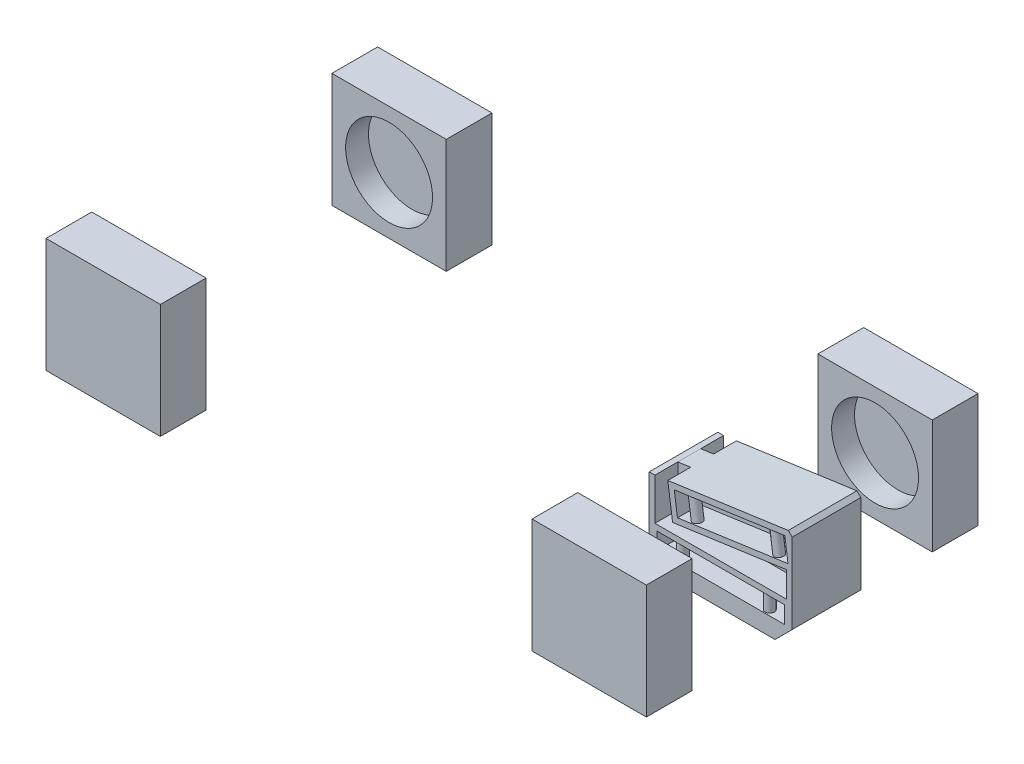
SolidWorks part; units mm, degrees
ref_plane "Front Plane" through (0, 0, 0) normal (0, 0, 1) x (1, 0, 0)
ref_plane "Top Plane" through (0, 0, 0) normal (0, 1, 0) x (1, 0, 0)
ref_plane "Right Plane" through (0, 0, 0) normal (1, 0, 0) x (0, 0, -1)
sketch "Sketch1" plane through (0, 0, 0) normal (0, 1, 0) x (1, 0, 0)
  line L0 (0, 175.6005) -> (0, -163.1385) construction
  line L1 (-212.5, -125) -> (212.5, -125)
  line L2 (-212.5, -125) -> (-212.5, 125)
  line L3 (-212.5, 125) -> (212.5, 125)
  line L4 (212.5, -125) -> (212.5, 125)
  line L5 (-212.5, -125) -> (212.5, 125) construction
  line L6 (-212.5, 125) -> (212.5, -125) construction
  line L7 (162.5, 105) -> (262.5, 105)
  line L8 (162.5, 105) -> (162.5, 145)
  line L9 (162.5, 145) -> (262.5, 145)
  line L10 (262.5, 105) -> (262.5, 145)
  line L11 (162.5, 105) -> (262.5, 145) construction
  line L12 (162.5, 145) -> (262.5, 105) construction
  line L13 (162.5, -105) -> (262.5, -105)
  line L14 (162.5, -105) -> (162.5, -145)
  line L15 (162.5, -145) -> (262.5, -145)
  line L16 (262.5, -105) -> (262.5, -145)
  line L17 (162.5, -105) -> (262.5, -145) construction
  line L18 (162.5, -145) -> (262.5, -105) construction
  line L19 (-231.0788, 0) -> (285.5483, 0) construction
  line L20 (-162.5, -145) -> (-262.5, -145)
  line L21 (-262.5, -105) -> (-262.5, -145)
  line L22 (-162.5, -105) -> (-262.5, -105)
  line L23 (-162.5, -105) -> (-162.5, -145)
  line L24 (-162.5, 145) -> (-262.5, 145)
  line L25 (-262.5, 105) -> (-262.5, 145)
  line L26 (-162.5, 105) -> (-262.5, 105)
  line L27 (-162.5, 105) -> (-162.5, 145)
  point P0 (0, 0)
  dimension "D1" = 425
  dimension "D2" = 250
  dimension "D3" = 100
  dimension "D4" = 40
  dimension "D5" = 40
  dimension "D6" = 100
extrude "Boss-Extrude1" add sketch "Sketch1" along normal mid plane 100 contours L3 L27 L24 L25 L26 L2 | L26 L27 L3 L2 | L7 L10 L9 L8 L3 L4 | L8 L7 L4 L3 | L16 L13 L4 L1 L14 L15 | L23 L1 L2 L22 L21 L20 | L23 L22 L2 L1
sketch "Sketch3" plane through (0, 0, 105) normal (0, 0, -1) x (-1, 0, 0)
  line L0 (-212.5, 50) -> (-212.5, -50) construction
  line L1 (-162.5, 50) -> (-262.5, 50) construction
  line L2 (-162.5, -50) -> (-262.5, -50) construction
  line L3 (-262.5, 0) -> (-162.5, 0) construction
  line L4 (-262.5, 50) -> (-262.5, -50) construction
  line L5 (-162.5, 50) -> (-162.5, -50) construction
  circle A0 centre (-212.5, 0) radius 38
  dimension "D1" = 76
extrude "Cut-Extrude5" cut sketch "Sketch3" against normal blind 20
sketch "Sketch4" plane through (0, 0, -105) normal (0, 0, 1) x (1, 0, 0)
  circle A0 centre (212.5, 0) radius 38 construction
  circle A1 centre (212.5, 0) radius 38
extrude "Cut-Extrude6" cut sketch "Sketch4" against normal blind 20
sketch3d "3DSketch4" plane through (0, 0, 0) normal (0, 0, 1) x (1, 0, 0)
  dimension "D1" = 8.42
sketch "Mech Trail & Caster" plane through (0, 0, 116.58) normal (0, 0, -1) x (-1, 0, 0)
  line L0 (-212.5, 38) -> (-212.5, -50) construction
  line L1 (-250.5, 0) -> (-174.5, 0) construction
  line L2 (-162.5, -50) -> (-262.5, -50) construction
  line L3 (-162.5, -50) -> (-262.5, -50)
  line L4 (-208.5, -50) -> (-212.5, -27) construction
  line L5 (-212.5, -27) -> (-225.6719, 48.7387) construction
  line L6 (-162.5, 50) -> (-262.5, 50) construction
  line L7 (-162.5, 50) -> (-262.5, 50)
  circle A0 centre (-212.5, 0) radius 38 construction
  circle A1 centre (-212.5, 0) radius 38
  point P7 (-212.5, -27)
  point P15 (-221.8913, 27)
  dimension "D1" = 23
  dimension "D2" = 4
  dimension "D3" = 23
  dimension "D4" = 9.866
sketch3d "3DSketch5"
  line L0 (212.5, 38, 116.58) -> (212.5, -50, 116.58) construction
  line L1 (250.5, 0, 116.58) -> (174.5, 0, 116.58) construction
sketch "Sketch6" plane through (221.8913, 0, 0) normal (1, 0, 0) x (0, 0, -1)
  line L0 (-116.58, 27) -> (-110.904, 27) construction
  point P0 (-116.58, 27)
  point P5 (-110.904, 27)
  dimension "D1" = 5.676
sketch3d "KPI angle/ steering axis"
  line L0 (221.8913, 27, 110.904) -> (212.5, -27, 116.58) construction
  point P0 (221.8913, 27, 110.904)
  point P2 (212.5, -27, 116.58)
sketch3d "3DSketch8" plane through (0, 0, 0) normal (0, 0, 1) x (1, 0, 0)
  dimension "D1" = 8.42
sketch "Sketch7" plane through (0, 0, -116.58) normal (0, 0, 1) x (1, 0, 0)
  line L0 (212.5, 50) -> (212.5, -50) construction
  line L1 (162.5, 50) -> (262.5, 50) construction
  line L2 (162.5, -50) -> (262.5, -50) construction
  line L3 (162.5, 0) -> (262.5, 0) construction
  line L4 (162.5, 50) -> (162.5, -50) construction
  line L5 (262.5, 50) -> (262.5, -50) construction
  line L6 (221.8913, 27) -> (212.5, -27) construction
  line L7 (221.8913, 27) -> (212.5, -27) construction
  point P12 (212.5, -27)
  point P13 (221.8913, 27)
sketch3d "3DSketch9"
  line L0 (212.5, 50, -116.58) -> (212.5, -50, -116.58) construction
  line L1 (162.5, 0, -116.58) -> (262.5, 0, -116.58) construction
sketch "Sketch8" plane through (221.8913, 0, 0) normal (-1, 0, 0) x (0, 0, 1)
  line L0 (-116.58, 27) -> (-110.91, 27) construction
  point P0 (-116.58, 27)
  point P5 (-110.91, 27)
  dimension "D1" = 5.67
sketch3d "3DSketch10"
  line L0 (221.8913, 27, -110.91) -> (212.5, -27, -116.58) construction
sketch3d "3DSketch11"
  line L0 (221.8913, 27, -116.58) -> (221.8913, 27, -110.91) construction
  line L1 (212.5, 50, -105) -> (212.5, -50, -105) construction
  line L2 (162.5, 50, -105) -> (262.5, 50, -105) construction
  line L3 (162.5, -50, -105) -> (262.5, -50, -105) construction
sketch "Front view IC's/RC" plane through (212.5, 0, 0) normal (-1, 0, 0) x (0, 0, 1)
  line L0 (-110.91, 27) -> (-89.7206, 27) construction
  line L1 (-110.91, 27) -> (285.7, -26.9974) construction
  line L2 (110.904, 27) -> (85.1327, 27) construction
  line L3 (110.904, 27) -> (-285.706, -26.9974) construction
  line L4 (-125, 50) -> (-125, -50) construction
  line L5 (-105, 50) -> (-145, 50) construction
  line L6 (-105, -50) -> (-145, -50) construction
  line L7 (125, 50) -> (125, -50) construction
  line L8 (105, 50) -> (145, 50) construction
  line L9 (105, -50) -> (145, -50) construction
  line L10 (-285.706, -26.9974) -> (285.7, -26.9974) construction
  line L11 (-125, -50) -> (285.7, -26.9974) construction
  line L12 (-285.706, -26.9974) -> (125, -50) construction
  line L13 (0, 78.2039) -> (0, -138.8888) construction
  point P20 (-116.58, -27)
  point P21 (116.58, -27)
  point P29 (0, -42.999)
  dimension "D1" = 7.753
  dimension "D2" = 396.61
  dimension "D3" = 7.753
  dimension "D4" = 396.61
  dimension "D5" = 7.001
  dimension "D6" = 410.706
sketch3d "3DSketch12" plane through (0, 0, 0) normal (0, 0, 1) x (1, 0, 0)
  dimension "D1" = 20
sketch "Left side IC's/PC" plane through (0, 0, -125) normal (0, 0, -1) x (-1, 0, 0)
  line L0 (162.5, -50) -> (262.5, -50) construction
  line L1 (162.5, 50) -> (262.5, 50) construction
  line L2 (162.5, -50) -> (262.5, -50)
  line L3 (162.5, 50) -> (262.5, 50)
  line L4 (212.5, 50) -> (212.5, -50) construction
  line L5 (162.5, 0) -> (262.5, 0) construction
  line L6 (162.5, 50) -> (162.5, -50) construction
  line L7 (262.5, 50) -> (262.5, -50) construction
  line L8 (-212.5, 50) -> (-212.5, -50) construction
  line L9 (-212.5, 50) -> (-212.5, -50) construction
  line L10 (-393.1005, -27) -> (329.5904, -27) construction
  line L11 (-221.8913, 27) -> (400.1441, -57.6885) construction
  line L12 (-221.8913, 27) -> (-156.9239, 27) construction
  line L13 (212.5, 27) -> (-344.6875, -61.2498) construction
  line L14 (212.5, 27) -> (147.1014, 27) construction
  line L15 (-212.5, -50) -> (174.7378, -27) construction
  line L16 (-128.4426, -27) -> (212.5, -50) construction
  point P12 (212.5, 27)
  point P13 (212.5, -27)
  point P14 (-212.5, -27)
  point P18 (13.51, -36.5761)
  point P27 (-128.4426, -27)
  point P29 (174.7378, -27)
  point P33 (-221.8913, 27)
  dimension "D1" = 23
  dimension "D2" = 54
  dimension "D3" = 7.753
  dimension "D4" = 9
  dimension "D5" = 340.9426
  dimension "D6" = 387.2378
  dimension "D7" = 13.4239
  dimension "D8" = 226.01
sketch3d "3DSketch13" plane through (0, 0, 0) normal (0, 0, 1) x (1, 0, 0)
  dimension "D1" = 20
sketch "Right side IC's/PC" plane through (0, 0, 125) normal (0, 0, -1) x (-1, 0, 0)
  line L0 (212.5, 50) -> (212.5, -50) construction
  line L1 (-221.8913, 27) -> (309.2663, -45.3157) construction
  line L2 (-221.8913, 27) -> (-150.1998, 27) construction
  line L3 (212.5, 27) -> (-297.8803, -53.8363) construction
  line L4 (162.5, -50) -> (262.5, -50)
  line L5 (262.5, -50) -> (262.5, 50)
  line L6 (262.5, 50) -> (162.5, 50)
  line L7 (162.5, 50) -> (162.5, -50)
  line L8 (162.5, -50) -> (262.5, -50)
  line L9 (262.5, -50) -> (262.5, 50)
  line L10 (262.5, 50) -> (162.5, 50)
  line L11 (162.5, 50) -> (162.5, -50)
  line L12 (212.5, 27) -> (139.4199, 27) construction
  line L13 (-212.5, -27) -> (212.5, -27) construction
  line L20 (-212.5, 50) -> (-212.5, -50) construction
  line L21 (-212.5, -50) -> (174.7378, -27) construction
  line L22 (212.5, -50) -> (-128.4426, -27) construction
  point P6 (212.5, -27)
  point P7 (212.5, 27)
  point P8 (-221.8913, 27)
  point P10 (174.7378, -27)
  point P24 (13.51, -36.5761)
  point P29 (-128.4426, -27)
  dimension "D2" = 23
  dimension "D3" = 54
  dimension "D4" = 7.753
  dimension "D5" = 9
  dimension "D6" = 340.9426
  dimension "D7" = 387.2378
  dimension "D8" = 13.4239
  dimension "D1" = 0
sketch3d "3DSketch14" plane through (0, 0, 0) normal (0, 0, 1) x (1, 0, 0)
  dimension "D1" = 50
sketch "Rear view IC's/RC" plane through (-212.5, 0, 0) normal (1, 0, 0) x (0, 0, -1)
  line L0 (-125, 50) -> (-125, -50) construction
  line L1 (-105, 50) -> (-145, 50) construction
  line L2 (-105, -50) -> (-145, -50) construction
  line L3 (125, 50) -> (125, -50) construction
  line L4 (105, 50) -> (145, 50) construction
  line L5 (105, -50) -> (145, -50) construction
  line L6 (0, 69.5621) -> (0, -61.9838) construction
  line L7 (-193.1722, -27) -> (206.3811, -27) construction
  line L8 (-110.91, 27) -> (114.5883, -27) construction
  line L9 (-110.91, 27) -> (-74.4999, 27) construction
  line L10 (110.91, 27) -> (79.0484, 27) construction
  line L11 (110.91, 27) -> (-114.5883, -27) construction
  line L12 (-125, -50) -> (114.5883, -27) construction
  line L13 (-114.5883, -27) -> (125, -50) construction
  point P12 (-110.91, 27)
  point P13 (-110.91, -27)
  point P17 (110.91, -27)
  point P18 (110.91, 27)
  point P26 (0, -38.0002)
  point P28 (114.5883, -27)
  point P30 (-114.5883, -27)
  dimension "D1" = 23
  dimension "D2" = 14.09
  dimension "D3" = 54
  dimension "D4" = 13.467
  dimension "D5" = 13.467
  dimension "D6" = 239.5883
  dimension "D7" = 11.9998
sketch3d "Chassis hardpoint plane LF upper "
  line L0 (-174.7378, -27, -125) -> (212.5, -26.9974, 285.7) construction
  point P0 (212.5, -26.9974, 285.7)
  point P2 (-174.7378, -27, -125)
  point P6 (221.8913, 27, -110.91)
sketch3d "Chassis hardpoint plane RF upper"
  line L0 (-174.7378, -27, 125) -> (212.5, -26.9974, -285.706) construction
  point P0 (221.8913, 27, 110.904)
  point P2 (212.5, -26.9974, -285.706)
  point P4 (-174.7378, -27, 125)
sketch3d "Chassis hardpoint plane RF/LF & LR/RR lower"
  line L0 (-174.7378, -27, 125) -> (212.5, -26.9974, -285.706) construction
  point P0 (212.5, -27, 116.58)
  point P2 (212.5, -26.9974, -285.706)
  point P4 (-174.7378, -27, 125)
sketch3d "Chassis hardpoint plane RR upper"
  line L0 (-212.5, -27, -114.5883) -> (128.4426, -27, 125) construction
  point P0 (-212.5, 27, 110.91)
  point P2 (128.4426, -27, 125)
  point P4 (-212.5, -27, -114.5883)
sketch3d "Chassis hardpoint plane LR upper"
  line L0 (-212.5, -27, 114.5883) -> (128.4426, -27, -125) construction
  point P0 (-212.5, -27, 114.5883)
  point P2 (-212.5, 27, -110.91)
  point P5 (128.4426, -27, -125)
sketch "Sketch11" plane through (0, 0, 0) normal (0, 0, 1) x (1, 0, 0)
  line L0 (150, 50) -> (150, -50)
  line L1 (150, -50) -> (275, -50)
  line L2 (275, -50) -> (275, 50)
  line L3 (275, 50) -> (150, 50)
  line L4 (212.5, 50) -> (212.5, -50) construction
  line L5 (162.5, 50) -> (262.5, 50) construction
  line L6 (162.5, -50) -> (262.5, -50) construction
  dimension "D2" = 125
extrude "Boss-Extrude3" add sketch "Sketch11" along normal mid plane 60 separate body
chamfer "Chamfer1" distance 15 angle 45 4 edges at (150, -50, 0) (150, 50, 0) (275, -50, 0) (275, 50, 0)
sketch "Sketch12" plane through (2.578, -18.301, -2.4306) normal (-0.1383, 0.9818, 0.1304) x (0.9904, 0.1371, 0.0182)
  line L0 (221.4412, 113.4993) -> (175.0618, 1.5295) construction
  line L1 (221.4412, 113.4993) -> (259.6574, 21.2372) construction
  line L2 (221.4412, 113.4993) -> (221.4412, 16.1167) construction
  point P0 (221.4412, 113.4993)
  dimension "D1" = 45
  dimension "D4" = 22.5
sketch3d "3DSketch17"
  line L0 (221.8913, 27, -110.91) -> (175.9576, 5.9002, -0.7593) construction
  line L1 (221.8913, 27, -110.91) -> (221.8913, 14.179, -14.375) construction
  line L2 (221.8913, 27, -110.91) -> (259.7403, 20.0924, -18.7551) construction
  line L3 (221.8913, 27, -110.91) -> (188.1512, 11.5014, -30)
  line L4 (221.8913, 27, -110.91) -> (221.8913, 14.179, -14.375)
  line L5 (221.8913, 27, -110.91) -> (255.1219, 20.9352, -30)
  line L14 (260, -50, -30) -> (165, -50, -30)
  line L15 (165, -50, -30) -> (150, -35, -30)
  line L16 (150, -35, -30) -> (150, 35, -30)
  line L17 (150, 35, -30) -> (165, 50, -30)
  line L18 (165, 50, -30) -> (260, 50, -30)
  line L19 (260, 50, -30) -> (275, 35, -30)
  line L20 (275, 35, -30) -> (275, -35, -30)
  line L21 (275, -35, -30) -> (260, -50, -30)
  line L22 (260, -50, -30) -> (165, -50, -30)
  line L23 (165, -50, -30) -> (150, -35, -30)
  line L24 (150, -35, -30) -> (150, 35, -30)
  line L25 (150, 35, -30) -> (165, 50, -30)
  line L26 (165, 50, -30) -> (260, 50, -30)
  line L27 (260, 50, -30) -> (275, 35, -30)
  line L28 (275, 35, -30) -> (275, -35, -30)
  line L29 (275, -35, -30) -> (260, -50, -30)
  dimension "D1" = 0
sketch "Sketch14" plane through (0, 0, -30) normal (0, 0, -1) x (-1, 0, 0)
  line L0 (-255.1219, 20.9352) -> (-188.1512, 11.5014) construction
  line L1 (-268.5804, 32.9298) -> (-271.3702, 13.1253)
  line L2 (-271.3702, 13.1253) -> (-174.6927, -0.4932)
  line L3 (-174.6927, -0.4932) -> (-171.9029, 19.3113)
  line L4 (-171.9029, 19.3113) -> (-268.5804, 32.9298)
  point P0 (-188.1512, 11.5014)
  point P2 (-255.1219, 20.9352)
  dimension "D1" = 15
  dimension "D2" = 15
  dimension "D3" = 20
sketch3d "3DSketch19"
sketch "Sketch15" plane through (0, -27, 0) normal (0, -1, 0) x (-1, 0, 0)
  line L0 (-212.5, -116.58) -> (-170.4048, -14.9533) construction
  line L1 (-212.5, -116.58) -> (-254.5952, -14.9533) construction
  line L2 (-212.5, -116.58) -> (-212.5, -17.7791) construction
  point P0 (-212.5, -116.58)
  dimension "D1" = 22.5
  dimension "D4" = 45
sketch3d "3DSketch20" plane through (0, 0, 0) normal (0, 0, 1) x (1, 0, 0)
sketch "Sketch16" plane through (0, 0, 30) normal (0, 0, 1) x (1, 0, 0)
  line L0 (212.5, -27) -> (254.5952, -27) construction
  line L1 (212.5, -27) -> (170.4048, -27) construction
  line L2 (212.5, -27) -> (254.5952, -27)
  line L3 (212.5, -27) -> (170.4048, -27)
sketch3d "3DSketch21"
  line L0 (212.5, -27, 116.58) -> (170.4048, -27, 14.9533) construction
  line L1 (212.5, -27, 30) -> (170.4048, -27, 30) construction
  line L2 (212.5, -27, 30) -> (254.5952, -27, 30) construction
  line L3 (212.5, -27, 116.58) -> (170.4048, -27, 14.9533) construction
  line L4 (212.5, -27, 30) -> (170.4048, -27, 30) construction
  line L5 (212.5, -27, 30) -> (254.5952, -27, 30) construction
  line L6 (212.5, -27, 116.58) -> (254.5952, -27, 14.9533) construction
  line L7 (212.5, -27, 116.58) -> (254.5952, -27, 14.9533) construction
  point P4 (176.6374, -27, 30)
  point P7 (248.3626, -27, 30)
sketch "Sketch17" plane through (0, 0, 30) normal (0, 0, 1) x (1, 0, 0)
  line L2 (176.6374, -27) -> (248.3626, -27) construction
  line L4 (156.6374, -19.5) -> (156.6374, -34.5)
  line L5 (156.6374, -34.5) -> (268.3626, -34.5)
  line L6 (268.3626, -34.5) -> (268.3626, -19.5)
  line L7 (268.3626, -19.5) -> (156.6374, -19.5)
  point P2 (248.3626, -27)
  point P5 (176.6374, -27)
  dimension "D1" = 20
  dimension "D2" = 20
  dimension "D3" = 15
extrude "Cut-Extrude8" cut sketch "Sketch17" against normal blind 20
sketch "Sketch22" plane through (0, -34.5, 0) normal (0, 1, 0) x (1, 0, 0)
  line L0 (212.5, -116.58) -> (254.5952, -14.9533) construction
  line L1 (212.5, -116.58) -> (170.4048, -14.9533) construction
  line L2 (212.5, -116.58) -> (254.5952, -14.9533) construction
  line L3 (212.5, -116.58) -> (170.4048, -14.9533) construction
  line L5 (212.5, -30) -> (212.5, -10) construction
  line L8 (156.6374, -30) -> (268.3626, -30)
  line L9 (268.3626, -30) -> (268.3626, -10)
  line L10 (268.3626, -10) -> (156.6374, -10)
  line L11 (156.6374, -10) -> (156.6374, -30)
  line L12 (156.6374, -30) -> (268.3626, -30)
  line L13 (268.3626, -30) -> (268.3626, -10)
  line L14 (268.3626, -10) -> (156.6374, -10)
  line L15 (156.6374, -10) -> (156.6374, -30)
  circle A0 centre (174.5663, -25) radius 4
  circle A1 centre (250.4337, -25) radius 4
  point P9 (174.5663, -25)
  dimension "D2" = 8
  dimension "D4" = 5
  dimension "D1" = 0
extrude "Boss-Extrude5" add sketch "Sketch22" along normal up to surface (15 mm away) contours L3 A0 | L3 A0 | A1 L2 | A1 L2
mirror "Mirror4" about plane through (0, 0, 0) normal (0, 0, 1) of "Boss-Extrude5", "Cut-Extrude8"
sketch3d "3DSketch22"
  line L0 (221.8913, 27, -110.91) -> (188.1512, 11.5014, -30) construction
  line L1 (221.8913, 27, -110.91) -> (255.1219, 20.9352, -30) construction
  line L2 (221.8913, 27, -110.91) -> (188.1512, 11.5014, -30)
  line L3 (221.8913, 27, -110.91) -> (255.1219, 20.9352, -30)
  line L4 (255.1219, 20.9352, -30) -> (262.5406, 19.5813, -11.9369) construction
  line L5 (188.1512, 11.5014, -30) -> (181.2784, 8.3444, -13.5189) construction
extrude "Cut-Extrude9" cut sketch "Sketch14" against normal blind 20
sketch "Sketch24" plane through (3.4671, -24.6129, 0) normal (-0.1395, 0.9902, 0) x (0.9902, 0.1395, 0)
  line L0 (255.548, 30) -> (262.7053, 11.9369) construction
  line L1 (255.548, 30) -> (262.7053, 11.9369) construction
  line L2 (187.9161, 30) -> (180.6702, 13.5189) construction
  line L4 (270.548, 30) -> (172.9161, 30)
  line L5 (172.9161, 30) -> (172.9161, 10)
  line L6 (172.9161, 10) -> (270.548, 10)
  line L7 (270.548, 10) -> (270.548, 30)
  line L8 (270.548, 30) -> (172.9161, 30)
  line L9 (172.9161, 30) -> (172.9161, 10)
  line L10 (172.9161, 10) -> (270.548, 10)
  line L11 (270.548, 10) -> (270.548, 30)
  line L13 (187.9161, 30) -> (180.6702, 13.5189) construction
  line L16 (221.732, 30) -> (221.732, 10) construction
  circle A0 centre (185.7178, 25) radius 4
  circle A1 centre (257.7462, 25) radius 4
  dimension "D2" = 8
  dimension "D3" = 5
  dimension "D1" = 0
extrude "Boss-Extrude7" add sketch "Sketch24" along normal up to surface (20 mm away) contours A1 | A0 up to face at (220.2417, 26.1205, -20)
mirror "Mirror5" about plane through (0, 0, 0) normal (0, 0, 1) of "Boss-Extrude7", "Cut-Extrude9"
sketch "Sketch27" plane through (0, 0, 30) normal (0, 0, 1) x (1, 0, 0)
  line L0 (275, -14.5) -> (155, -14.5)
  line L1 (275, -35) -> (275, 35) construction
  line L2 (155, -14.5) -> (155, 21.9796)
  line L3 (155, 21.9796) -> (271.596, 38.404)
  line L4 (275, 35) -> (260, 50) construction
  line L5 (171.9029, 19.3113) -> (268.5804, 32.9298) construction
  line L6 (268.3626, -19.5) -> (156.6374, -19.5) construction
  line L7 (171.9029, 19.3113) -> (268.5804, 32.9298) construction
  line L8 (150, 35) -> (150, -35) construction
  line L9 (155, 21.9796) -> (150, 21.9796)
  line L10 (155, -14.5) -> (150, -14.5)
  line L11 (165, 50) -> (150, 35) construction
  line L12 (260, 50) -> (165, 50) construction
  line L13 (150, 35) -> (150, 21.9796)
  line L14 (165, 50) -> (150, 35)
  line L15 (271.596, 38.404) -> (260, 50)
  line L16 (260, 50) -> (165, 50)
  line L17 (150, 35) -> (150, -14.5)
  line L18 (150, 21.9796) -> (150, -14.5)
  line M8 (150, 35) -> (150, -35)
  line M13 (275, 35) -> (260, 50)
  line M14 (260, 50) -> (165, 50)
  line M15 (165, 50) -> (150, 35)
  dimension "D1" = 5
  dimension "D2" = 5
  dimension "D3" = 5
extrude "Cut-Extrude12" cut sketch "Sketch27" against normal up to surface (60 mm away) contours L9 L3 M13 M14 M15 M8 up to face at (221.6365, 16.2183, -30)
sketch "Sketch28" plane through (0, 0, 30) normal (0, 0, 1) x (1, 0, 0)
  line L0 (275, -35) -> (275, 35) construction
  line L1 (275, -14.5) -> (155, -14.5) construction
  line L2 (155, -14.5) -> (155, 21.9796) construction
  line L3 (155, 21.9796) -> (271.596, 38.404) construction
  line L7 (275, -35) -> (275, -14.5)
  line L8 (270, -14.5) -> (155, -14.5)
  line L9 (155, -14.5) -> (155, 21.9796)
  line L10 (155, 21.9796) -> (166.2544, 23.565)
  line L14 (166.2544, 23.565) -> (170.439, -6.1417)
  line L15 (174.6927, -0.4932) -> (171.9029, 19.3113) construction
  line L16 (174.6927, -0.4932) -> (171.9029, 19.3113) construction
  line L17 (271.3702, 13.1253) -> (174.6927, -0.4932) construction
  line L18 (170.439, -6.1417) -> (270, 7.883)
  line L19 (270, 7.883) -> (270, -14.5)
  line L20 (271.3702, 13.1253) -> (174.6927, -0.4932) construction
  line M16 (271.596, 38.404) -> (155, 21.9796)
  dimension "D1" = 5
  dimension "D3" = 5
  dimension "D4" = 5
extrude "Cut-Extrude13" cut sketch "Sketch28" against normal blind 20 contours L19 L18 L14 L9 L8 M16
mirror "Mirror6" about plane through (0, 0, 0) normal (0, 0, 1) of "Cut-Extrude13"
sketch "Sketch29" plane through (0, 0, -105) normal (0, 0, 1) x (1, 0, 0)
  line L0 (-212.5, 50) -> (-212.5, -50) construction
  line L1 (-162.5, 50) -> (-262.5, 50) construction
  line L2 (-162.5, -50) -> (-262.5, -50) construction
  line L3 (-262.5, 0) -> (-162.5, 0) construction
  line L4 (-262.5, 50) -> (-262.5, -50) construction
  line L5 (-162.5, 50) -> (-162.5, -50) construction
  circle A0 centre (-212.5, 0) radius 38
  dimension "D1" = 76
extrude "Cut-Extrude14" cut sketch "Sketch29" against normal blind 20 and the other way blind 230
sketch3d "3DSketch23" plane through (0, 0, 0) normal (0, 0, 1) x (1, 0, 0)
  dimension "D1" = 25
sketch "Sketch31" plane through (-5.4746, -32.5324, 7.7905) normal (-0.1615, -0.9597, 0.2298) x (-0.9869, 0.1571, -0.0376)
  line L0 (241.3253, -14.7194) -> (149.6351, -11.1732)
  line L2 (209.7794, -114.1483) -> (211.1489, -78.7394) construction
sketch "Sketch32" plane through (0, 0, 25) normal (0, 0, 1) x (1, 0, 0)
  line L0 (-243.6318, 8.7992) -> (-153.1452, -6.428) construction
  line L1 (-250.0528, 9.8797) -> (-123.5148, -11.4142)
sketch "Sketch33" plane through (221.8913, 0, 0) normal (-1, 0, 0) x (0, 0, 1)
  line L0 (-110.91, 27) -> (-25, 15.3036) construction
  line L1 (-110.91, 27) -> (-62.6591, 27) construction
  dimension "D1" = 85.91
  dimension "D2" = 7.753
sketch3d "3DSketch24"
sketch "Sketch34" plane through (2.2035, -15.6428, 0) normal (0.1395, -0.9902, 0) x (-0.9902, -0.1395, 0)
  line L0 (-223.4882, 110.91) -> (-221.8567, 25) construction
  line L1 (-223.4882, 110.91) -> (-257.1768, 25) construction
  point P0 (-223.4882, 110.91)
  point P1 (-221.8567, 25)
  dimension "D1" = 22.5
sketch3d "3DSketch25"
  line L0 (221.8913, 27, -110.91) -> (256.8661, 20.2303, -25)
sketch "Sketch35" plane through (2.2035, -15.6428, 0) normal (0.1395, -0.9902, 0) x (-0.9902, -0.1395, 0)
  line L0 (-223.4882, 110.91) -> (-221.8567, 25) construction
  line L1 (-223.4882, 110.91) -> (-221.8567, 25) construction
  line L2 (-223.4882, 110.91) -> (-185.9765, 25) construction
  dimension "D1" = 22.5
sketch3d "3DSketch26"
  line L0 (221.8913, 27, -110.91) -> (186.3619, 10.2987, -25)
sketch3d "3DSketch27"
sketch "Sketch36" plane through (0, -27, 0) normal (0, -1, 0) x (-1, 0, 0)
  line L0 (-250.4337, 25) -> (-174.5663, 25) construction
  line L1 (-212.5, 116.58) -> (-250.4337, 25)
  line L2 (-212.5, 116.58) -> (-174.5663, 25)
  circle A0 centre (-174.5663, 25) radius 4 construction
  circle A1 centre (-250.4337, 25) radius 4 construction
  circle A2 centre (-174.5663, 25) radius 4
  circle A3 centre (-250.4337, 25) radius 4
  point P0 (-212.5, 116.58)
